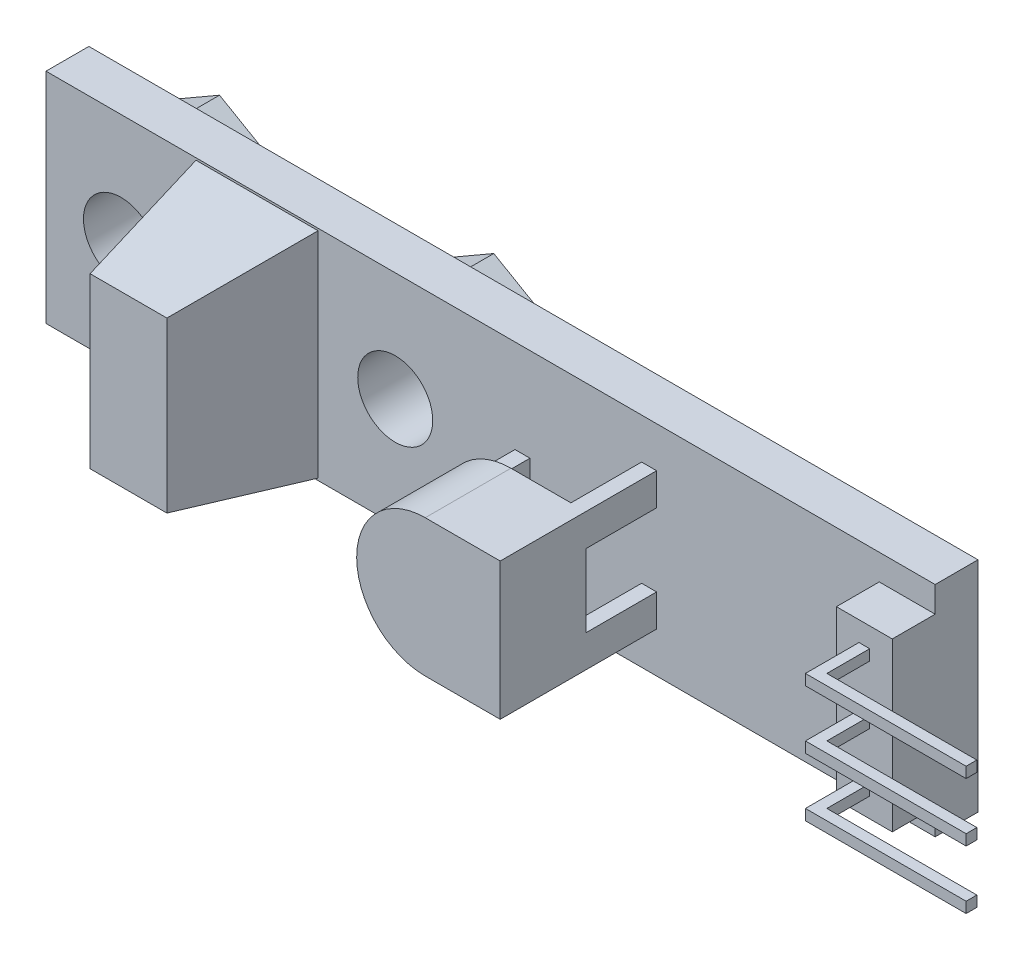
SolidWorks part; units mm, degrees
ref_plane "Plano frontal" through (0, 0, 0) normal (0, 0, 1) x (1, 0, 0)
ref_plane "Plano superior" through (0, 0, 0) normal (0, 1, 0) x (1, 0, 0)
ref_plane "Plano direito" through (0, 0, 0) normal (1, 0, 0) x (0, 0, -1)
sketch "Esboço1" plane through (0, 0, 0) normal (0, 0, 1) x (1, 0, 0)
  line L1 (-20.75, 5.1) -> (20.75, 5.1)
  line L2 (-20.75, 5.1) -> (-20.75, -5.1)
  line L3 (-20.75, -5.1) -> (20.75, -5.1)
  line L4 (20.75, 5.1) -> (20.75, -5.1)
  line L5 (-20.75, 5.1) -> (20.75, -5.1) construction
  line L6 (-20.75, -5.1) -> (20.75, 5.1) construction
  circle A0 centre (-17.25, 0) radius 1.75
  circle A1 centre (-4.45, 0) radius 1.75
  point P0 (0, 0)
  dimension "D3" = 3.5
  dimension "D4" = 3.5
  dimension "D1" = 41.5
  dimension "D2" = 10.2
  dimension "D5" = 16.3
extrude "Ressalto-extrusão1" add sketch "Esboço1" along normal blind 2
sketch "Esboço2" plane through (0, 0, 2) normal (0, 0, 1) x (1, 0, 0)
  line L0 (-20.75, 5.1) -> (-20.75, -5.1) construction
  line L1 (-13.75, -5) -> (-8.05, -5)
  line L2 (-13.75, -5) -> (-13.75, 5)
  line L3 (-13.75, 5) -> (-8.05, 5)
  line L4 (-8.05, -5) -> (-8.05, 5)
  line L5 (-13.75, -5) -> (-8.05, 5) construction
  line L6 (-13.75, 5) -> (-8.05, -5) construction
  point P0 (-10.9, 0)
  dimension "D1" = 5.7
  dimension "D2" = 10
  dimension "D3" = 7
extrude "Ressalto-extrusão2" add sketch "Esboço2" along normal blind 6 draft 10
sketch "Esboço3" plane through (0, 0, 2) normal (0, 0, 1) x (1, 0, 0)
  line L0 (4.25, 3.2) -> (7.75, 3.2)
  line L1 (7.75, 3.2) -> (7.75, -3.2)
  line L2 (7.75, -3.2) -> (4.25, -3.2)
  line L3 (20.75, -5.1) -> (20.75, 5.1) construction
  arc A0 (4.25, 3.2) -> (4.25, -3.2) centre (4.25, 0) ccw
  dimension "D1" = 6.4
  dimension "D3" = 13
  dimension "D2" = 3.5
extrude "Ressalto-extrusão3" add sketch "Esboço3" along normal blind 7.3
sketch "Esboço4" plane through (0, 0, 9.3) normal (0, 0, 1) x (1, 0, 0)
  line L0 (7.05, -3.2) -> (7.05, -1.7)
  line L1 (7.05, -1.7) -> (7.75, -1.7)
  line L2 (1.1391, 0.75) -> (1.8391, 0.75)
  line L3 (4.25, -3.2) -> (7.75, -3.2)
  line L4 (7.75, -3.2) -> (7.75, 3.2)
  line L5 (7.75, 3.2) -> (4.25, 3.2)
  line L6 (4.25, -3.2) -> (7.05, -3.2)
  line L7 (7.75, -1.7) -> (7.75, 1.7)
  line L8 (7.05, 3.2) -> (4.25, 3.2)
  line L9 (1.8391, 0.75) -> (1.8391, -0.75)
  line L10 (1.8391, -0.75) -> (1.1391, -0.75)
  line L11 (0, 0) -> (8.7292, 0) construction
  line L12 (7.05, 3.2) -> (7.05, 1.7)
  line L13 (7.05, 1.7) -> (7.75, 1.7)
  arc A0 (1.1391, -0.75) -> (4.25, -3.2) centre (4.25, 0) ccw
  arc A1 (4.25, 3.2) -> (4.25, -3.2) centre (4.25, 0) ccw
  arc A2 (4.25, 3.2) -> (1.1391, 0.75) centre (4.25, 0) ccw
  dimension "D2" = 1.5
  dimension "D3" = 0.7
  dimension "D4" = 1.5
  dimension "D5" = 0.7
  dimension "D1" = 0
extrude "Corte-extrusão1" cut sketch "Esboço4" against normal up to surface (3.3 mm away) from offset 4 up to face at (-15.5, 0, 2) offset against normal yes
sketch "Esboço6" plane through (0, 0, 0) normal (0, 1, 0) x (1, 0, 0)
  line L0 (18.1412, -2) -> (18.1412, -4)
  line L1 (-20.75, -2) -> (20.75, -2) construction
  line L2 (18.1412, -4) -> (19.1956, -4)
  line L3 (20.75, -4) -> (20.75, -2)
  line L4 (20.75, -2) -> (18.1412, -2)
  line L5 (19.1956, -4) -> (19.1956, -6.5)
  line L6 (19.1956, -6.5) -> (26.6956, -6.5)
  line L7 (26.6956, -6.5) -> (26.6956, -6)
  line L8 (26.6956, -6) -> (19.6956, -6)
  line L9 (19.6956, -6) -> (19.6956, -4)
  line L10 (19.6956, -4) -> (20.75, -4)
  dimension "D1" = 7.5
  dimension "D2" = 4.5
  dimension "D3" = 0.5
  dimension "D4" = 0.5
  dimension "D5" = 2
extrude "Ressalto-extrusão4" add sketch "Esboço6" along normal mid plane 7.8
sketch "Esboço7" plane through (0, 0, 6.5) normal (0, 0, 1) x (1, 0, 0)
  line L0 (26.6956, 3.9) -> (26.6956, 2.9785)
  line L1 (26.6956, 3.9) -> (26.6956, -3.9) construction
  line L2 (26.6956, 2.9785) -> (19.1956, 2.9785)
  line L3 (19.1956, 3.9) -> (19.1956, -3.9) construction
  line L4 (19.1956, 2.9785) -> (19.1956, 3.9)
  line L5 (19.1956, 3.9) -> (26.6956, 3.9)
  line L6 (26.6956, 2.4785) -> (19.1956, 2.4785)
  line L7 (19.1956, 2.4785) -> (19.1956, 0.25)
  line L8 (19.1956, 3.9) -> (19.1956, -3.9) construction
  line L9 (19.1956, 0.25) -> (26.6956, 0.25)
  line L10 (26.6956, 0.25) -> (26.6956, 2.4785)
  line L11 (19.1956, 0) -> (28.7836, 0) construction
  line L12 (26.6956, 2.9785) -> (26.6956, 2.4785) construction
  line L13 (26.6956, 2.9785) -> (26.6956, 2.4785) construction
  line L14 (26.6956, 0.25) -> (26.6956, -0.25) construction
  line L15 (26.6956, -2.9785) -> (26.6956, -2.4785) construction
  line L16 (26.6956, -0.25) -> (26.6956, -2.4785)
  line L17 (19.1956, -0.25) -> (26.6956, -0.25)
  line L18 (19.1956, -2.4785) -> (19.1956, -0.25)
  line L19 (26.6956, -2.4785) -> (19.1956, -2.4785)
  line L20 (19.1956, -3.9) -> (26.6956, -3.9)
  line L21 (19.1956, -2.9785) -> (19.1956, -3.9)
  line L22 (26.6956, -2.9785) -> (19.1956, -2.9785)
  line L23 (26.6956, -3.9) -> (26.6956, -2.9785)
  line L24 (26.6956, -2.4785) -> (26.6956, -2.9785) construction
  dimension "D1" = 0.5
extrude "Corte-extrusão2" cut sketch "Esboço7" against normal up to surface (2.5 mm away) up to face at (18.6684, 0, 4)
sketch "Esboço8" plane through (0, 0, 0) normal (0, 0, -1) x (-1, 0, 0)
  line L1 (7.55, 1.7898) -> (4.45, 3.5796)
  line L2 (4.45, 3.5796) -> (1.35, 1.7898)
  line L3 (1.35, 1.7898) -> (1.35, -1.7898)
  line L4 (1.35, -1.7898) -> (4.45, -3.5796)
  line L5 (4.45, -3.5796) -> (7.55, -1.7898)
  line L6 (7.55, -1.7898) -> (7.55, 1.7898)
  line L7 (14.15, -1.7898) -> (17.25, -3.5796)
  line L8 (17.25, -3.5796) -> (20.35, -1.7898)
  line L9 (20.35, -1.7898) -> (20.35, 1.7898)
  line L10 (20.35, 1.7898) -> (17.25, 3.5796)
  line L11 (17.25, 3.5796) -> (14.15, 1.7898)
  line L12 (14.15, 1.7898) -> (14.15, -1.7898)
  circle A0 centre (4.45, 0) radius 3.1 construction
  circle A1 centre (17.25, 0) radius 3.1 construction
  circle A2 centre (4.45, 0) radius 1.75
  circle A3 centre (17.25, 0) radius 1.75
  dimension "D1" = 6.2
extrude "Ressalto-extrusão5" add sketch "Esboço8" along normal blind 2.6
